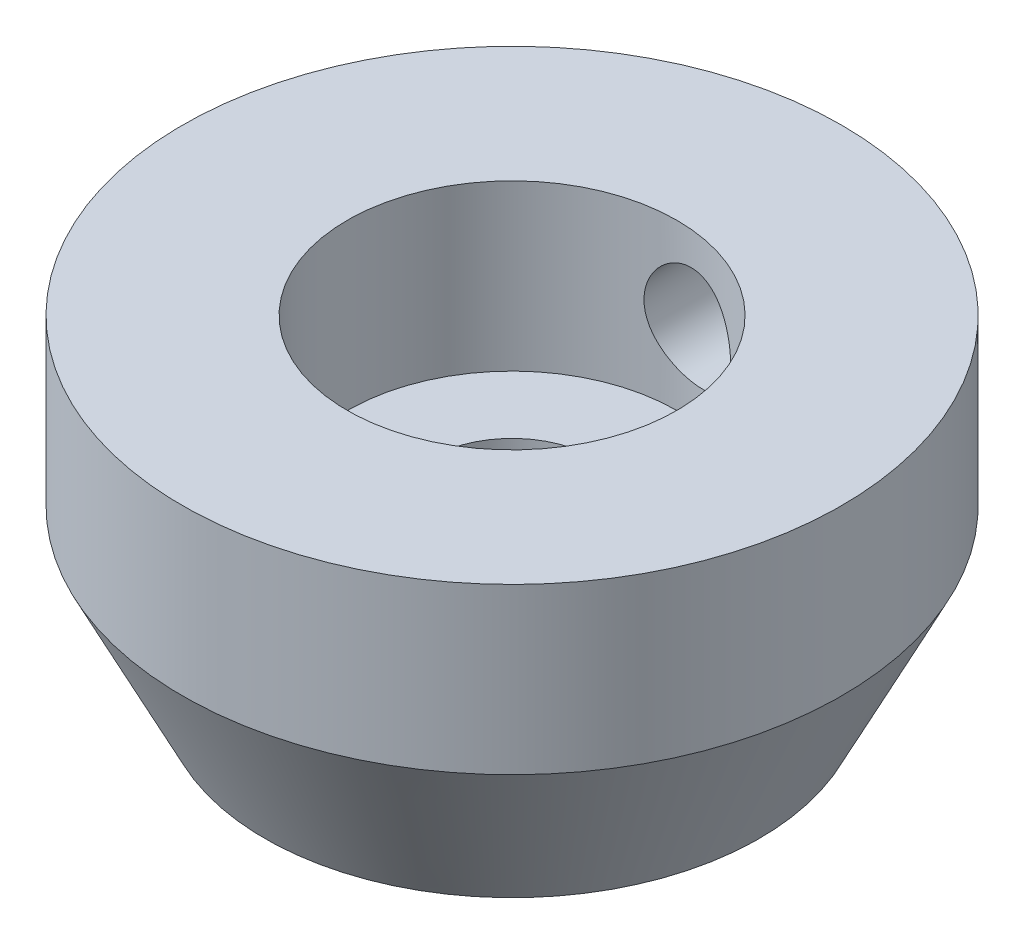
SolidWorks part; units mm, degrees
ref_plane "Front Plane" through (0, 0, 0) normal (0, 0, 1) x (1, 0, 0)
ref_plane "Top Plane" through (0, 0, 0) normal (0, 1, 0) x (1, 0, 0)
ref_plane "Right Plane" through (0, 0, 0) normal (1, 0, 0) x (0, 0, -1)
sketch "Sketch1" plane through (0, 0, 0) normal (0, 0, 1) x (1, 0, 0)
  line L0 (-1.1728, 0) -> (-1.1728, 32.5926) construction
  line L1 (8.8272, 15.3086) -> (18.8272, 15.3086)
  line L2 (18.8272, 15.3086) -> (18.8272, 5.3086)
  line L3 (18.8272, 5.3086) -> (13.8272, -4.6914)
  line L4 (13.8272, -4.6914) -> (3.8272, -4.6914)
  line L5 (3.8272, -4.6914) -> (3.8272, 5.3086)
  line L6 (8.8272, 15.3086) -> (8.8272, 5.3086)
  line L7 (8.8272, 5.3086) -> (3.8272, 5.3086)
  dimension "D1" = 10
  dimension "D2" = 5
  dimension "D3" = 10
  dimension "D4" = 10
  dimension "D5" = 10
  dimension "D6" = 10
revolve "Revolve1" add sketch "Sketch1" angle 360 about L0
sketch "Sketch2" plane through (0, 0, 0) normal (0, 0, 1) x (1, 0, 0)
  line L0 (8.8272, 15.3086) -> (-11.1728, 15.3086) construction
  circle A0 centre (0, 10.3086) radius 3
  dimension "D1" = 5
extrude "Cut-Extrude1" cut sketch "Sketch2" against normal blind 23
